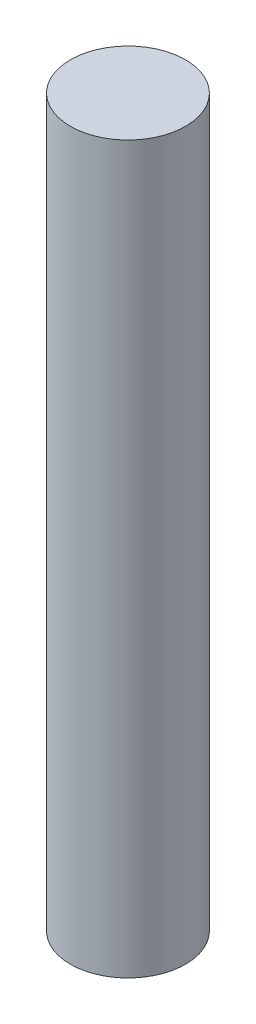
SolidWorks part; units mm, degrees
material "AISI 1020"
ref_plane "Front Plane" through (0, 0, 0) normal (0, 0, 1) x (1, 0, 0)
ref_plane "Top Plane" through (0, 0, 0) normal (0, 1, 0) x (1, 0, 0)
ref_plane "Right Plane" through (0, 0, 0) normal (1, 0, 0) x (0, 0, -1)
sketch "Sketch1" plane through (0, 0, 0) normal (0, 1, 0) x (1, 0, 0)
  circle A0 centre (0, 0) radius 12.7
  dimension "D1" = 25.4
extrude "Boss-Extrude1" add sketch "Sketch1" along normal blind 160
